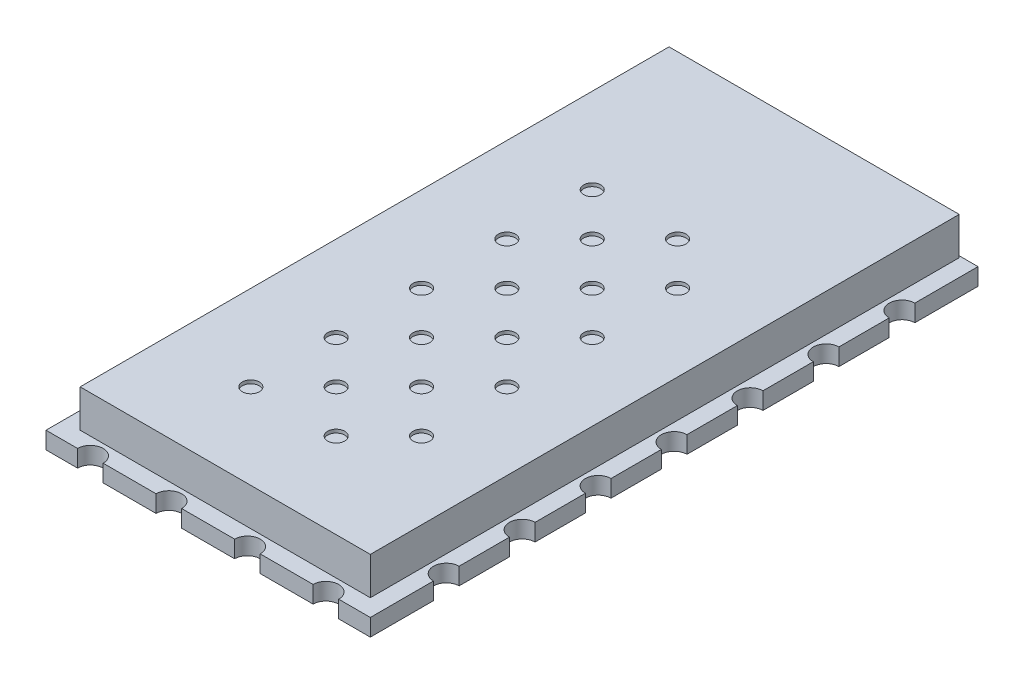
SolidWorks part; units mm, degrees
ref_plane "Plan de face" through (0, 0, 0) normal (0, 0, 1) x (1, 0, 0)
ref_plane "Plan de dessus" through (0, 0, 0) normal (0, 1, 0) x (1, 0, 0)
ref_plane "Plan de droite" through (0, 0, 0) normal (1, 0, 0) x (0, 0, -1)
sketch "Esquisse1" plane through (0, 0, 0) normal (0, 1, 0) x (1, 0, 0)
  line L1 (0, 0) -> (19, 0)
  line L2 (0, 0) -> (0, 35.6)
  line L3 (0, 35.6) -> (19, 35.6)
  line L4 (19, 0) -> (19, 35.6)
  dimension "D1" = 19
  dimension "D2" = 35.6
extrude "Boss.-Extru.1" add sketch "Esquisse1" along normal blind 1
sketch "Esquisse2" plane through (0, 1, 0) normal (0, 1, 0) x (1, 0, 0)
  line L0 (0, 0) -> (19, 0) construction
  line L1 (1, 35.5) -> (18, 35.5)
  line L2 (1, 35.5) -> (1, 1)
  line L3 (1, 1) -> (18, 1)
  line L4 (18, 35.5) -> (18, 1)
  line L5 (0, 35.6) -> (0, 0) construction
  line L6 (19, 0) -> (19, 35.6) construction
  line L7 (19, 35.6) -> (0, 35.6) construction
  dimension "D1" = 1
  dimension "D2" = 1
  dimension "D3" = 1
  dimension "D4" = 0.1
extrude "Boss.-Extru.2" add sketch "Esquisse2" along normal blind 2.2
sketch "Esquisse3" plane through (0, 3.2, 0) normal (0, 1, 0) x (1, 0, 0)
  line L0 (1, 35.5) -> (1, 1) construction
  line L1 (1, 1) -> (18, 1) construction
  circle A0 centre (6, 6) radius 0.5
  circle A1 centre (8.5, 6) radius 0.5 [skipped]
  circle A2 centre (11, 6) radius 0.5
  circle A3 centre (13.5, 6) radius 0.5 [skipped]
  circle A4 centre (8.5, 8.5) radius 0.5
  circle A5 centre (11, 8.5) radius 0.5 [skipped]
  circle A6 centre (13.5, 8.5) radius 0.5
  circle A7 centre (8.5, 11) radius 0.5 [skipped]
  circle A8 centre (11, 11) radius 0.5
  circle A9 centre (13.5, 11) radius 0.5 [skipped]
  circle A10 centre (8.5, 13.5) radius 0.5
  circle A11 centre (11, 13.5) radius 0.5 [skipped]
  circle A12 centre (13.5, 13.5) radius 0.5
  circle A13 centre (8.5, 16) radius 0.5 [skipped]
  circle A14 centre (11, 16) radius 0.5
  circle A15 centre (13.5, 16) radius 0.5 [skipped]
  circle A16 centre (8.5, 18.5) radius 0.5
  circle A17 centre (11, 18.5) radius 0.5 [skipped]
  circle A18 centre (13.5, 18.5) radius 0.5
  circle A19 centre (8.5, 21) radius 0.5 [skipped]
  circle A20 centre (11, 21) radius 0.5
  circle A21 centre (13.5, 21) radius 0.5 [skipped]
  circle A22 centre (8.5, 23.5) radius 0.5
  circle A23 centre (11, 23.5) radius 0.5 [skipped]
  circle A24 centre (13.5, 23.5) radius 0.5
  circle A25 centre (8.5, 26) radius 0.5 [skipped]
  circle A26 centre (11, 26) radius 0.5
  circle A27 centre (13.5, 26) radius 0.5 [skipped]
  circle A28 centre (6, 8.5) radius 0.5 [skipped]
  circle A29 centre (6, 11) radius 0.5
  circle A30 centre (6, 13.5) radius 0.5 [skipped]
  circle A31 centre (6, 16) radius 0.5
  circle A32 centre (6, 18.5) radius 0.5 [skipped]
  circle A33 centre (6, 21) radius 0.5
  circle A34 centre (6, 23.5) radius 0.5 [skipped]
  circle A35 centre (6, 26) radius 0.5
  dimension "D1" = 1
  dimension "D2" = 5
  dimension "D3" = 5
  dimension "D4" = 4
  dimension "D5" = 9
extrude "Enlèv. mat.-Extru.1" cut sketch "Esquisse3" against normal blind 0.2
sketch "Esquisse4" plane through (0, 1, 0) normal (0, 1, 0) x (1, 0, 0)
  line L0 (0, 0) -> (19, 0) construction
  line L2 (0, 35.6) -> (0, 0) construction
  line L4 (9.5, 0) -> (9.5, 35.5) construction
  line L5 (18, 35.5) -> (1, 35.5) construction
  circle A0 centre (2.6, 0) radius 0.75
  circle A1 centre (7.2, 0) radius 0.75
  circle A2 centre (11.8, 0) radius 0.75
  circle A3 centre (16.4, 0) radius 0.75
  circle A4 centre (0, 4.45) radius 0.75
  circle A5 centre (0, 8.9) radius 0.75
  circle A6 centre (0, 13.35) radius 0.75
  circle A7 centre (0, 17.8) radius 0.75
  circle A8 centre (0, 22.25) radius 0.75
  circle A9 centre (0, 26.7) radius 0.75
  circle A10 centre (0, 31.15) radius 0.75
  circle A11 centre (19, 4.45) radius 0.75
  circle A12 centre (19, 8.9) radius 0.75
  circle A13 centre (19, 13.35) radius 0.75
  circle A14 centre (19, 17.8) radius 0.75
  circle A15 centre (19, 22.25) radius 0.75
  circle A16 centre (19, 26.7) radius 0.75
  circle A17 centre (19, 31.15) radius 0.75
  dimension "D1" = 1.5
  dimension "D2" = 2.6
  dimension "D4" = 4.45
  dimension "D3" = 4
  dimension "D5" = 7
extrude "Enlèv. mat.-Extru.2" cut sketch "Esquisse4" against normal through all
